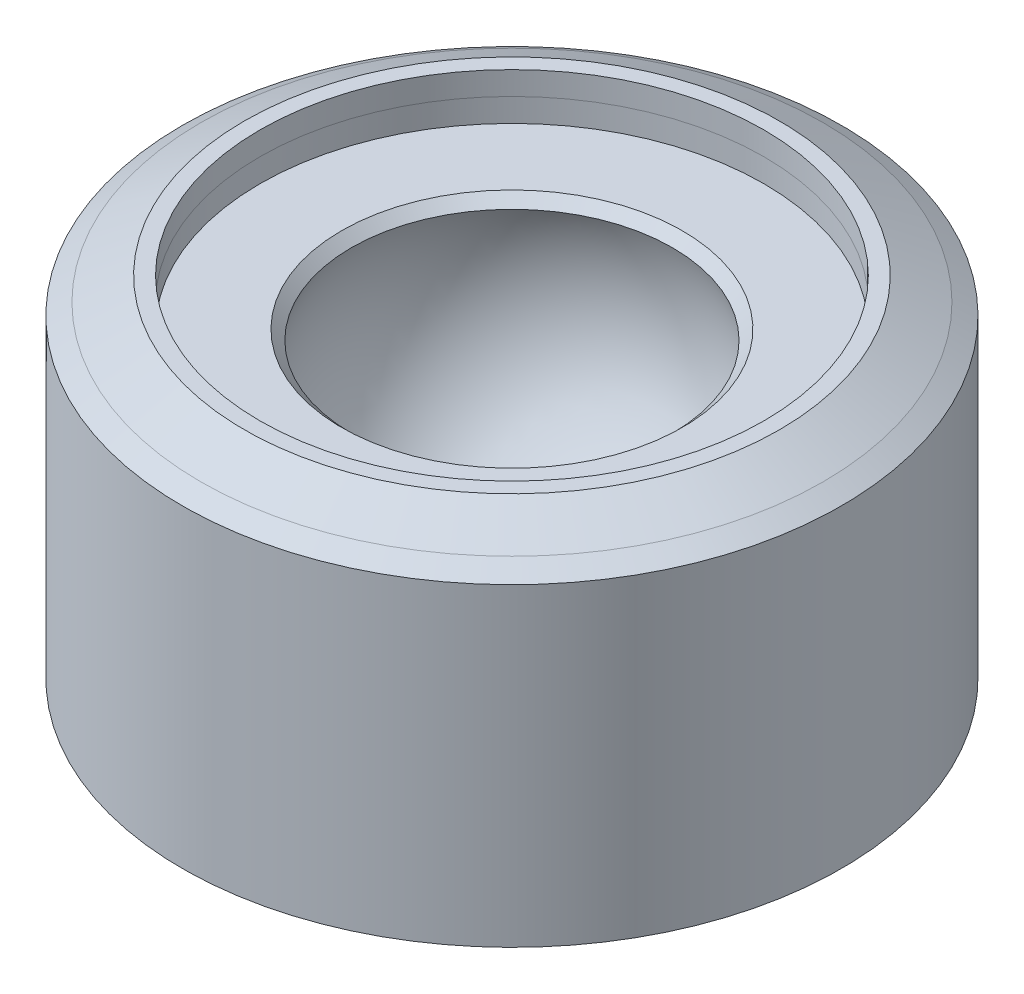
SolidWorks part; units mm, degrees
material "AISI 4340 Steel, normalized"
ref_plane "Front Plane" through (0, 0, 0) normal (0, 0, 1) x (1, 0, 0)
ref_plane "Top Plane" through (0, 0, 0) normal (0, 1, 0) x (1, 0, 0)
ref_plane "Right Plane" through (0, 0, 0) normal (1, 0, 0) x (0, 0, -1)
sketch "Sketch1" plane through (0, 0, 0) normal (0, 0, 1) x (1, 0, 0)
  line L0 (-19.5138, 23.33) -> (-19.5138, 26.33)
  line L1 (-19.5138, 26.33) -> (-21.5138, 26.33)
  line L2 (-21.5138, 26.33) -> (-27.1384, 23.33)
  line L3 (-29.5138, -18.67) -> (12.9862, -18.67)
  line L8 (-19.5138, 23.33) -> (-19.4985, 20.33)
  line L9 (-19.4985, 20.33) -> (-8.9911, 20.33)
  line L10 (-8.9911, 20.33) -> (-7.7249, 19.0652)
  line L11 (12.9862, -12.1477) -> (12.9862, -18.67)
  line L14 (-29.5138, -18.67) -> (-29.5138, 21.8352)
  line L15 (-29.5138, 21.8352) -> (-27.1384, 23.33)
  arc A1 (-7.7249, 19.0652) -> (12.9862, -12.1477) centre (12.9862, 10.33) ccw
  dimension "D2" = 42.5
revolve "Revolve1" add sketch "Sketch1" angle 360 about L11
